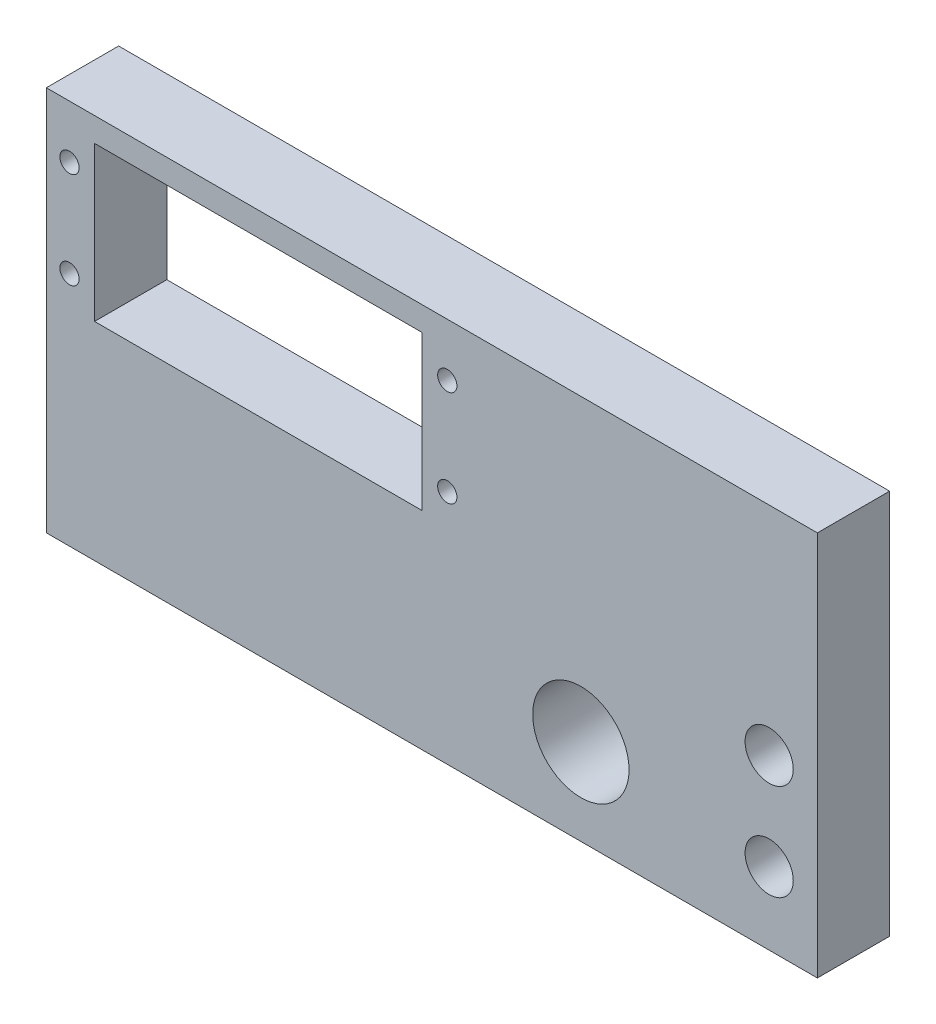
SolidWorks part; units mm, degrees
ref_plane "Front Plane" through (0, 0, 0) normal (0, 0, 1) x (1, 0, 0)
ref_plane "Top Plane" through (0, 0, 0) normal (0, 1, 0) x (1, 0, 0)
ref_plane "Right Plane" through (0, 0, 0) normal (1, 0, 0) x (0, 0, -1)
sketch "Sketch1" plane through (0, 0, 0) normal (0, 0, 1) x (1, 0, 0)
  line L0 (6.35, 37.465) -> (49.53, 37.465) construction
  line L1 (0, 0) -> (101.6, 0)
  line L2 (0, 0) -> (0, 50.8)
  line L3 (0, 50.8) -> (101.6, 50.8)
  line L4 (101.6, 0) -> (101.6, 50.8)
  line L5 (6.35, 47.625) -> (49.53, 47.625)
  line L6 (6.35, 47.625) -> (6.35, 27.305)
  line L7 (6.35, 27.305) -> (49.53, 27.305)
  line L8 (49.53, 47.625) -> (49.53, 27.305)
  line L9 (27.94, 47.625) -> (27.94, 27.305) construction
  circle A0 centre (95.25, 22.225) radius 3.175
  circle A1 centre (95.25, 9.525) radius 3.175
  circle A2 centre (3.048, 43.815) radius 1.27
  circle A3 centre (3.048, 31.115) radius 1.27
  circle A4 centre (52.832, 43.815) radius 1.27
  circle A5 centre (52.832, 31.115) radius 1.27
  circle A6 centre (70.4356, 11.3491) radius 6.35
  dimension "D2" = 6.35
  dimension "D12" = 12.7
  dimension "D14" = 2.54
  dimension "D16" = 12.7
  dimension "D1" = 101.6
  dimension "D3" = 12.7
  dimension "D4" = 9.525
  dimension "D5" = 50.8
  dimension "D6" = 20.32
  dimension "D7" = 43.18
  dimension "D8" = 6.35
  dimension "D9" = 3.175
  dimension "D10" = 49.784
  dimension "D11" = 49.784
  dimension "D13" = 12.7
  dimension "D15" = 6.35
extrude "Boss-Extrude1" add sketch "Sketch1" along normal blind 9.525
sketch "Sketch2" plane through (0, 0, 0) normal (0, -1, 0) x (1, 0, 0)
  line L0 (101.6, 9.525) -> (101.6, 0) construction
  line L1 (0, 4.7625) -> (101.6, 4.7625) construction
  line L2 (0, 9.525) -> (0, 0) construction
  line L3 (0, 0) -> (101.6, 0) construction
  circle A0 centre (60.2488, 4.7625) radius 1.7272
  circle A1 centre (79.2988, 4.7625) radius 1.7272
  point P4 (101.6, 4.7625)
  dimension "D1" = 3.4544
  dimension "D2" = 19.05
  dimension "D3" = 22.3012
  dimension "D4" = 4.7625
extrude "Cut-Extrude1" cut sketch "Sketch2" against normal blind 12.7
